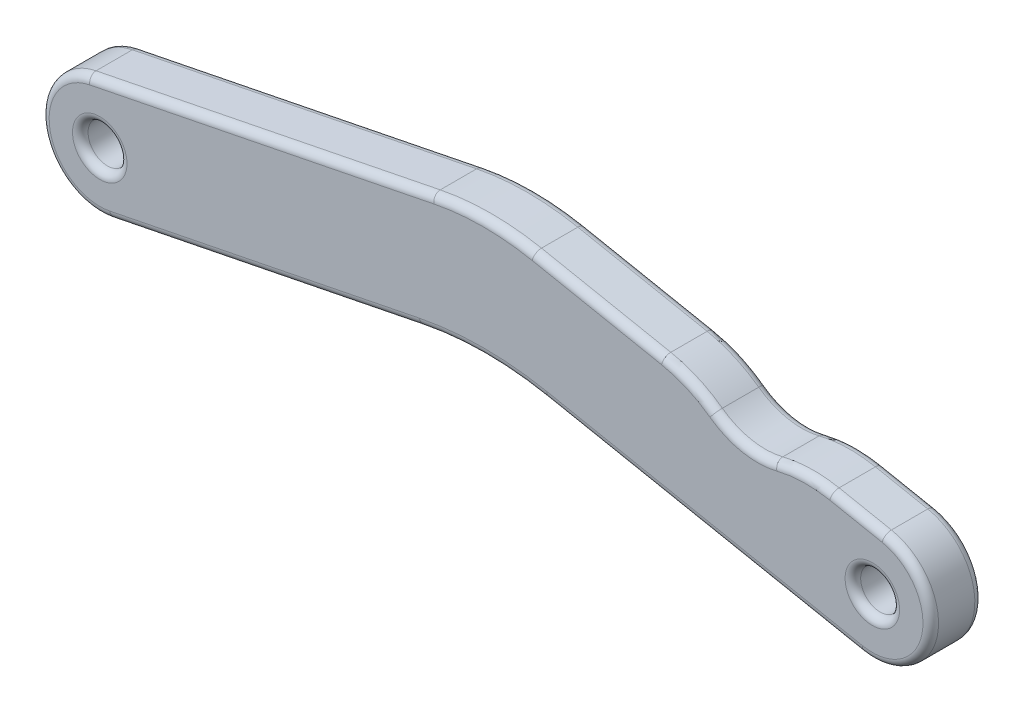
SolidWorks part; units mm, degrees
ref_plane "Front" through (0, 0, 0) normal (0, 0, 1) x (1, 0, 0)
ref_plane "Top" through (0, 0, 0) normal (0, 1, 0) x (1, 0, 0)
ref_plane "Right" through (0, 0, 0) normal (1, 0, 0) x (0, 0, -1)
sketch "Sketch1" plane through (0, 0, 0) normal (0, 0, 1) x (1, 0, 0)
  line L0 (0, 0) -> (29.7737, 0) construction
  line L1 (0, 2.25) -> (29.7737, 2.25)
  line L2 (0, -2.25) -> (29.7737, -2.25)
  circle A0 centre (0, 0) radius 0.75
  arc A1 (0, 2.25) -> (0, -2.25) centre (0, 0) ccw
  arc A2 (29.7737, -2.25) -> (29.7737, 2.25) centre (29.7737, 0) ccw
  circle A3 centre (29.7737, 0) radius 0.75
  point P3 (14.8869, 0)
  dimension "D1" = 1.5
  dimension "D2" = 29.7737
  dimension "D3" = 1.5
extrude "Boss-Extrude1" add sketch "Sketch1" along normal blind 2
sketch "Sketch2" plane through (0, 0, 0) normal (0, 0, 1) x (1, 0, 0)
  line L0 (12.0571, -0.5571) -> (14.4503, 0.4122)
  line L1 (15.3955, 0.2207) -> (16.4724, -0.5571)
  line L2 (16.4724, -0.5571) -> (17.3174, -2.6432)
  line L3 (17.3174, -2.6432) -> (12.0571, -3.2881)
  line L4 (12.0571, -3.2881) -> (12.0571, -0.5571)
  arc A0 (14.4503, 0.4122) -> (15.3955, 0.2207) centre (14.7783, -0.3977) cw
sketch "Sketch3" plane through (0, 0, 0) normal (0, 0, 1) x (1, 0, 0)
  line L0 (0.4422, -2.2061) -> (12.3757, 0.1857)
  line L1 (17.1839, 0.1926) -> (29.3379, -2.2074)
  line L2 (-0.4422, 2.2061) -> (12.8219, 4.8647)
  line L3 (16.7243, 4.8702) -> (30.2096, 2.2074)
  circle A0 centre (0, 0) radius 2.25 construction
  arc A1 (12.3757, 0.1857) -> (17.1839, 0.1926) centre (14.797, -11.8947) cw
  arc A2 (29.3379, -2.2074) -> (30.2096, 2.2074) centre (29.7737, 0) ccw
  arc A3 (29.7737, -2.25) -> (29.7737, 2.25) centre (29.7737, 0) ccw construction
  circle A4 centre (29.7737, 0) radius 0.75 construction
  arc A5 (0.4422, -2.2061) -> (-0.4422, 2.2061) centre (0, 0) cw
  arc A6 (0, 2.25) -> (0, -2.25) centre (0, 0) ccw construction
  arc A7 (12.8219, 4.8647) -> (16.7243, 4.8702) centre (14.7871, -4.9403) cw
  point P17 (12.41, 0.1926)
  point P26 (0, 0)
  dimension "D1" = 10
extrude "Cut-Extrude4" cut sketch "Sketch3" along normal through all flip side to cut
sketch "Sketch4" plane through (0, 0, 2) normal (0, 0, 1) x (1, 0, 0)
  line L4 (12.8219, 4.8647) -> (-0.4422, 2.2061)
  line L5 (30.2096, 2.2074) -> (16.7243, 4.8702)
  line L6 (17.1839, 0.1926) -> (29.3379, -2.2074)
  line L7 (0.4422, -2.2061) -> (12.3757, 0.1857)
  line L8 (12.8219, 4.8647) -> (-0.4422, 2.2061)
  line L9 (30.2096, 2.2074) -> (16.7243, 4.8702)
  line L10 (17.1839, 0.1926) -> (29.3379, -2.2074)
  line L11 (0.4422, -2.2061) -> (12.3757, 0.1857)
  circle A0 centre (29.7737, 0) radius 0.75 construction
  circle A1 centre (0, 0) radius 0.75 construction
  circle A2 centre (29.7737, 0) radius 0.75
  circle A3 centre (0, 0) radius 0.75
  arc A4 (16.7243, 4.8702) -> (12.8219, 4.8647) centre (14.7871, -4.9403) ccw
  arc A5 (29.3379, -2.2074) -> (30.2096, 2.2074) centre (29.7737, 0) ccw
  arc A6 (17.1839, 0.1926) -> (12.3757, 0.1857) centre (14.797, -11.8947) ccw
  arc A7 (-0.4422, 2.2061) -> (0.4422, -2.2061) centre (0, 0) ccw
  arc A8 (16.7243, 4.8702) -> (12.8219, 4.8647) centre (14.7871, -4.9403) ccw
  arc A9 (29.3379, -2.2074) -> (30.2096, 2.2074) centre (29.7737, 0) ccw
  arc A10 (17.1839, 0.1926) -> (12.3757, 0.1857) centre (14.797, -11.8947) ccw
  arc A11 (-0.4422, 2.2061) -> (0.4422, -2.2061) centre (0, 0) ccw
  dimension "D1" = 0
extrude "Boss-Extrude2" add sketch "Sketch4" against normal up to vertex
sketch3d "3DSketch2"
  line L8 (28.5539, 2.4862, 2) -> (20.7366, 4.2679, 2)
  line L9 (30.5553, 5.4776, 2) -> (31.9718, 1.7671, 2)
  line L10 (18.1052, 9.4862, 2) -> (17.7608, 10.5197, 2)
  line L11 (20.8202, 8.9829, 2) -> (18.1052, 9.4862, 2)
  arc A18 (30.4787, 0.5435, 2) -> (28.5539, 2.4862, 2) centre (27.9872, 0, 2) ccw
  arc A19 (29.7103, 7.668, 2) -> (30.5553, 5.4776, 2) centre (-281.7577, -113.7456, 2) ccw
  arc A20 (25.106, 12.1538, 2) -> (29.7103, 7.668, 2) centre (22.4753, 4.8477, 2) ccw
  arc A21 (21.1241, 8.8735, 2) -> (20.8202, 8.9829, 2) centre (20.6379, 7.9997, 2) ccw
  arc A22 (26.5449, 8.4396, 2) -> (21.1241, 8.8735, 2) centre (23.5636, 5.2719, 2) ccw
  arc A23 (25.3798, 7.2017, 2) -> (26.5449, 8.4396, 2) centre (25.9623, 7.8207, 2) ccw
  arc A24 (21.6394, 7.094, 2) -> (25.3798, 7.2017, 2) centre (23.5636, 5.2719, 2) ccw
  arc A25 (20.9991, 6.8287, 2) -> (21.6394, 7.094, 2) centre (21.0222, 7.6784, 2) ccw
  arc A26 (20.7366, 4.2679, 2) -> (20.9991, 6.8287, 2) centre (23.5636, 5.2719, 2) ccw
  spline S12 degree 3 poles (31.0836, 0.7536, 2) (30.8819, 0.6835, 2) (30.6803, 0.6135, 2) (30.4787, 0.5435, 2) knots 0 0 0 0 1 1 1 1
  spline S13 degree 3 poles (31.9718, 1.7671, 2) (31.9394, 1.656, 2) (31.8982, 1.5432, 2) (31.793, 1.3329, 2) (31.7287, 1.2339, 2) (31.5778, 1.0565, 2) (31.4894, 0.9764, 2) (31.2983, 0.8449, 2) (31.195, 0.7923, 2) (31.0836, 0.7536, 2) knots 0 0 0 0 0.25 0.25 0.5 0.5 0.75 0.75 1 1 1 1
  spline S14 degree 3 poles (21.9785, 12.5206, 2) (22.5054, 12.5209, 2) (23.0298, 12.4877, 2) (24.0747, 12.3695, 2) (24.5956, 12.2784, 2) (25.106, 12.1538, 2) knots 0 0 0 0 0.5 0.5 1 1 1 1
  spline S15 degree 3 poles (21.2302, 12.2749, 2) (21.4793, 12.3579, 2) (21.7264, 12.4476, 2) (21.9785, 12.5206, 2) knots 0 0 0 0 1 1 1 1
  spline S16 degree 3 poles (19.5527, 11.5132, 2) (19.7933, 11.7049, 2) (20.0675, 11.854, 2) (20.6399, 12.0887, 2) (20.9367, 12.1771, 2) (21.2302, 12.2749, 2) knots 0 0 0 0 0.5 0.5 1 1 1 1
  spline S17 degree 3 poles (17.7608, 10.5197, 2) (18.4099, 10.7525, 2) (19.009, 11.0801, 2) (19.5527, 11.5132, 2) knots 0 0 0 0 1 1 1 1
  point P53 (27.9872, 0, 4.55)
  point P54 (-281.7577, -113.7456, -332.2957)
  point P55 (22.4753, 4.8477, -5.7653)
  point P56 (20.6379, 7.9997, 3)
  point P57 (23.5636, 5.2719, 6.35)
  point P58 (25.9623, 7.8207, 2.85)
  point P59 (23.5636, 5.2719, -0.65)
  point P60 (21.0222, 7.6784, 2.85)
  point P61 (23.5636, 5.2719, -1)
sketch3d "3DSketch4"
  line L10 (30.2677, 2.5017, -2.25) -> (27.1133, 3.1246, -2.25)
  line L11 (29.9689, -6.5571, -2.25) -> (32.1516, -0.9209, -2.25)
  line L12 (14.2336, -12.4587, -2.25) -> (29.9689, -6.5571, -2.25)
  line L13 (13.1286, 5.8861, -2.25) -> (14.2336, -12.4587, -2.25)
  line L14 (22.8533, 6.935, -2.25) -> (13.1286, 5.8861, -2.25)
  arc A8 (32.1516, -0.9209, -2.25) -> (30.2677, 2.5017, -2.25) centre (29.7737, 0, -2.25) ccw
  arc A9 (23.4638, 3.6312, -2.25) -> (22.8533, 6.935, -2.25) centre (25.9576, 5.8004, -2.25) ccw
  arc A10 (26.4711, 3.0374, -2.25) -> (23.4638, 3.6312, -2.25) centre (25.3501, 5.2719, -2.25) ccw
  arc A11 (27.1133, 3.1246, -2.25) -> (26.4711, 3.0374, -2.25) centre (26.9195, 2.1435, -2.25) ccw
  point P25 (29.7737, 0, 0.3)
  point P26 (25.9576, 5.8004, -5.5552)
  point P27 (25.3501, 5.2719, -4.75)
  point P28 (26.9195, 2.1435, -1.25)
sketch "Sketch6" plane through (0, 0, 0) normal (0, 0, 1) x (1, 0, 0)
  line L6 (28.1927, 2.6057) -> (29.0519, 2.436)
  line L7 (30.2096, 2.2074) -> (16.7243, 4.8702) construction
  line L8 (21.7074, 3.8863) -> (20.9399, 4.0378)
  line L9 (29.0519, 2.436) -> (30.9007, 7.2749)
  line L10 (30.9007, 7.2749) -> (20.2741, 7.7153)
  line L11 (20.2741, 7.7153) -> (20.9399, 4.0378)
  arc A5 (23.6947, 3.0136) -> (26.0228, 2.5539) centre (25.3501, 5.2719) ccw
  arc A6 (23.4638, 3.6312) -> (26.4711, 3.0374) centre (25.3501, 5.2719) ccw construction
  arc A7 (28.1927, 2.6057) -> (26.0228, 2.5539) centre (27.224, -2.2996) ccw
  arc A8 (21.7074, 3.8863) -> (23.6947, 3.0136) centre (20.7388, -1.019) cw
  point P14 (26.8051, 2.8797)
  point P17 (23.095, 3.6123)
  dimension "D1" = 0.3
  dimension "D2" = 5
extrude "Cut-Extrude6" cut sketch "Sketch6" against normal through all and the other way through all
fillet "Fillet1" radius 0.3 28 edges at (30.5237, 0, 0) (0.75, 0, 0) (6.4089, -1.0102, 0) (14.7794, 0.426, 0) (23.2609, -1.0074, 0) (31.9811, -0.4359, 0) (14.7728, 5.0597, 2) (14.7728, 5.0597, 0) (6.1898, 3.5354, 2) (6.1898, 3.5354, 0) (-2.2061, -0.4422, 0) (30.5237, 0, 2) (0.75, 0, 2) (31.9811, -0.4359, 2) (23.2609, -1.0074, 2) (14.7794, 0.426, 2) (6.4089, -1.0102, 2) (-2.2061, -0.4422, 2) (19.2159, 4.3783, 2) (29.2011, 2.4065, 2) (24.8077, 2.525, 0) (22.749, 3.5591, 2) (24.8077, 2.525, 2) (27.1049, 2.699, 2)
